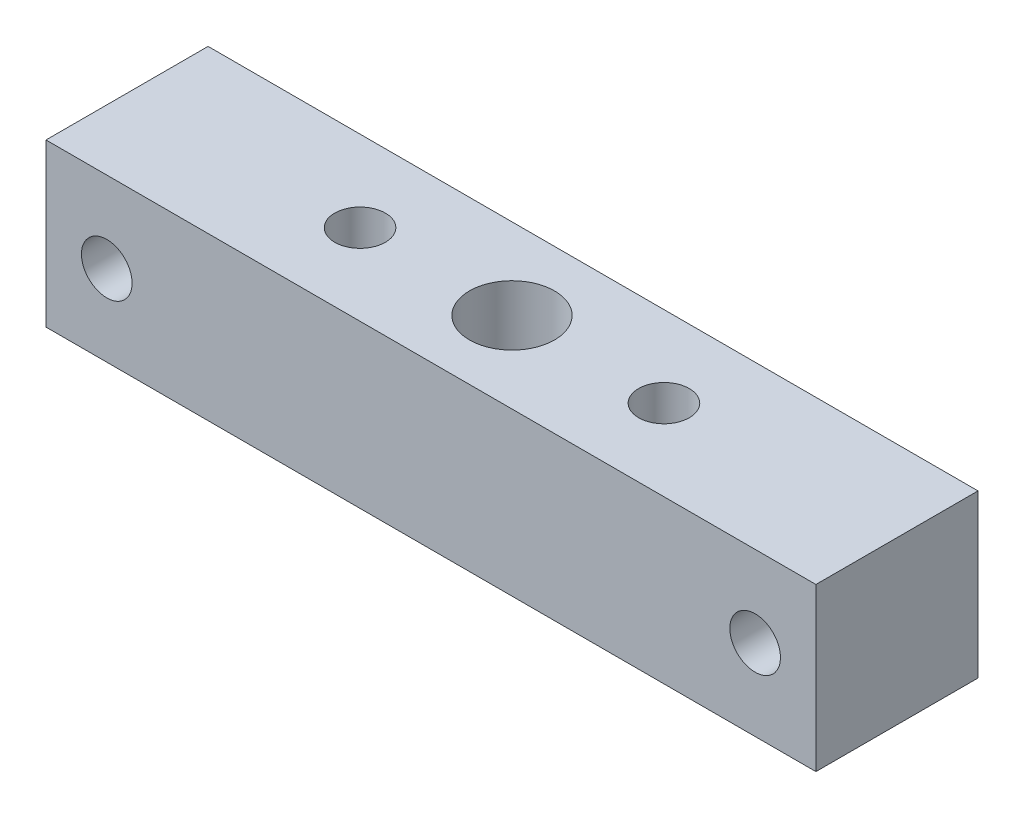
SolidWorks part; units mm, degrees
ref_plane "Front Plane" through (0, 0, 0) normal (0, 0, 1) x (1, 0, 0)
ref_plane "Top Plane" through (0, 0, 0) normal (0, 1, 0) x (1, 0, 0)
ref_plane "Right Plane" through (0, 0, 0) normal (1, 0, 0) x (0, 0, -1)
sketch "Sketch1" plane through (0, 0, 0) normal (0, 0, 1) x (1, 0, 0)
  line L1 (0, 0) -> (38, 0)
  line L2 (0, 0) -> (0, 8)
  line L3 (0, 8) -> (38, 8)
  line L4 (38, 0) -> (38, 8)
  dimension "D1" = 8
  dimension "D2" = 38
extrude "Boss-Extrude1" add sketch "Sketch1" along normal blind 8
hole_wizard "Tap Drill for M5x0.8 Tap1" positions "Sketch3" profile "Sketch2" hole size "M5x0.8" standard "Ansi Metric" end condition through all
sketch "Sketch3" plane through (0, 8, 0) normal (0, 1, 0) x (-1, 0, 0)
  line L0 (-19, 8) -> (-19, 0) construction
  line L1 (-38, 8) -> (0, 8) construction
  line L3 (-38, 0) -> (0, 0) construction
  point P0 (-19, 4)
sketch "Sketch2" plane through (19, 8, 4) normal (1, 0, 0) x (0, 0, 1)
  line L0 (0, 0) -> (0, 8)
  line L1 (0, 8) -> (2.1, 8)
  line L2 (2.1, 8) -> (2.1, 0)
  line L5 (2.1, 0) -> (0, 0)
  line L11 (0, -6.35) -> (0, 107.95) construction
  dimension "Thru Hole Dia." = 4.2
  dimension "Thru Hole Depth" = 8
cosmetic thread "Cosmetic Thread1" parameters "D2"=5
hole_wizard "Tap Drill for M3x0.5 Tap1" positions "Sketch5" profile "Sketch4" hole size "M3x0.5" standard "Ansi Metric" end condition through all
sketch "Sketch5" plane through (0, 0, 0) normal (0, 0, -1) x (-1, 0, 0)
  line L0 (-38, 4) -> (0, 4) construction
  line L1 (-38, 0) -> (-38, 8) construction
  line L2 (0, 8) -> (0, 0) construction
  line L4 (-19, 8) -> (-19, 0) construction
  line L5 (-38, 8) -> (0, 8) construction
  line L6 (0, 0) -> (-38, 0) construction
  point P0 (-35, 4)
  point P1 (-3, 4)
  dimension "D1" = 32
  dimension "D2" = 16
sketch "Sketch4" plane through (35, 4, 0) normal (1, 0, 0) x (0, 1, 0)
  line L0 (0, 0) -> (0, 8)
  line L1 (0, 8) -> (1.25, 8)
  line L2 (1.25, 8) -> (1.25, 0)
  line L5 (1.25, 0) -> (0, 0)
  line L11 (0, -6.35) -> (0, 107.95) construction
  dimension "Thru Hole Dia." = 2.5
  dimension "Thru Hole Depth" = 8
hole_wizard "Tap Drill for M3x0.5 Tap2" positions "Sketch8" profile "Sketch7" hole size "M3x0.5" standard "Ansi Metric" end condition through all
sketch "Sketch8" plane through (0, 8, 0) normal (0, 1, 0) x (-1, 0, 0)
  line L1 (0, 4) -> (-38, 4) construction
  line L2 (0, 8) -> (0, 0) construction
  line L3 (-38, 8) -> (-38, 0) construction
  circle A0 centre (-19, 4) radius 2.1 construction
  point P0 (-11.5, 4)
  point P1 (-26.5, 4)
  dimension "D1" = 7.5
  dimension "D2" = 15
sketch "Sketch7" plane through (11.5, 8, 4) normal (1, 0, 0) x (0, 0, 1)
  line L0 (0, 0) -> (0, 8)
  line L1 (0, 8) -> (1.25, 8)
  line L2 (1.25, 8) -> (1.25, 0)
  line L5 (1.25, 0) -> (0, 0)
  line L11 (0, -6.35) -> (0, 107.95) construction
  dimension "Thru Hole Dia." = 2.5
  dimension "Thru Hole Depth" = 8
